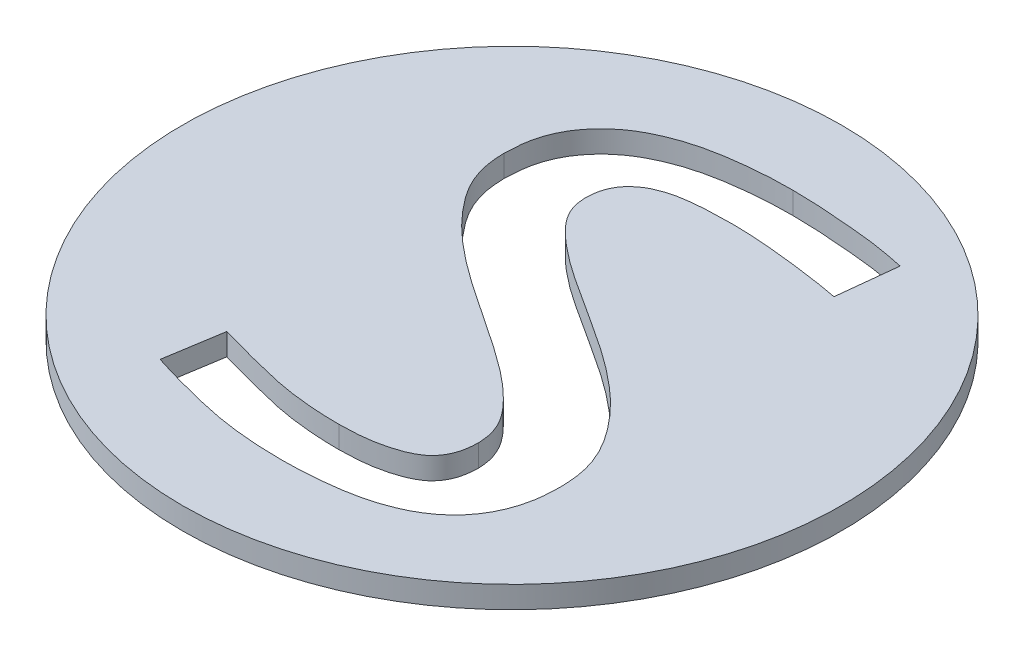
SolidWorks part; units mm, degrees
ref_plane "Front Plane" through (0, 0, 0) normal (0, 0, 1) x (1, 0, 0)
ref_plane "Top Plane" through (0, 0, 0) normal (0, 1, 0) x (1, 0, 0)
ref_plane "Right Plane" through (0, 0, 0) normal (1, 0, 0) x (0, 0, -1)
sketch "Sketch1" plane through (0, 0, 0) normal (0, 1, 0) x (1, 0, 0)
  circle A0 centre (0, 0) radius 45
  text T0 "S" font "3ds" height 65
  point P4 (0, 0)
  point P5 (-22.3112, -28.0814)
  point P6 (0, 0)
  point P7 (0, 0)
  point P8 (0, 0)
  point P9 (-25.1322, -31.9282)
  point P10 (0, 0)
  dimension "D1" = 90
extrude "Boss-Extrude1" add sketch "Sketch1" along normal blind 3
